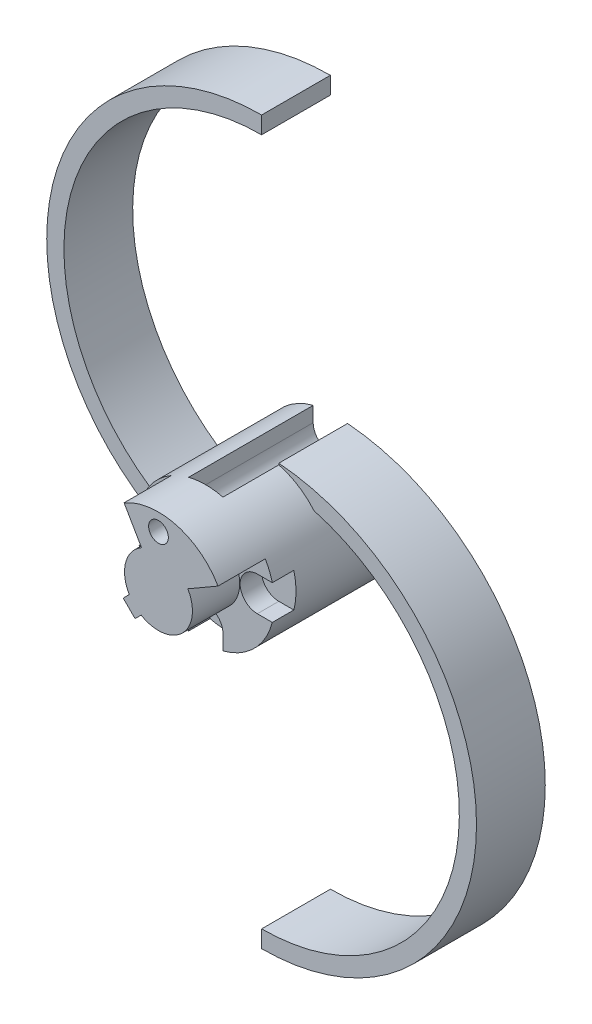
SolidWorks part; units mm, degrees
ref_plane "Front Plane" through (0, 0, 0) normal (0, 0, 1) x (1, 0, 0)
ref_plane "Top Plane" through (0, 0, 0) normal (0, 1, 0) x (1, 0, 0)
ref_plane "Right Plane" through (0, 0, 0) normal (1, 0, 0) x (0, 0, -1)
sketch "Leg-Sketch" plane through (0, 0, 0) normal (0, 0, 1) x (1, 0, 0)
  line L0 (0, 0) -> (0, -42) construction
  line L1 (0, -42) -> (0, -40)
  line L2 (0, 42) -> (0, 40)
  circle A0 centre (0, 0) radius 8 construction
  circle A1 centre (0, 0) radius 6 construction
  circle A2 centre (0, 6) radius 1.15
  circle A3 centre (-6, 0) radius 1.15
  circle A4 centre (0, -6) radius 1.15
  circle A5 centre (6, 0) radius 1.15
  arc A7 (0, 8) -> (0, -42) centre (0, -17) cw
  arc A8 (6.0995, 5.1765) -> (0, -40) centre (0, -17) cw
  arc A9 (0, -8) -> (6.0995, 5.1765) centre (0, 0) ccw
  arc A10 (0, -8) -> (0, 42) centre (0, 17) cw
  arc A11 (0, 40) -> (-6.0995, -5.1765) centre (0, 17) ccw
  arc A12 (0, 8) -> (-6.0995, -5.1765) centre (0, 0) ccw
  point P12 (0, 8)
  dimension "D1" = 16
  dimension "D2" = 12
  dimension "D3" = 2.3
  dimension "D4" = 2
  dimension "D5" = 50
extrude "Leg" add sketch "Leg-Sketch" along normal blind 8
sketch "Hub-Sketch" plane through (0, 0, 0) normal (0, 0, -1) x (-1, 0, 0)
  circle A0 centre (0, 0) radius 8
  circle A1 centre (0, 6) radius 1.15 construction
  circle A2 centre (-6, 0) radius 1.15 construction
  circle A3 centre (0, -6) radius 1.15 construction
  circle A4 centre (6, 0) radius 1.15 construction
  circle A5 centre (0, 6) radius 1.15
  circle A6 centre (-6, 0) radius 1.15
  circle A7 centre (0, -6) radius 1.15
  circle A8 centre (6, 0) radius 1.15
  arc A9 (6.0995, -5.1765) -> (0, 8) centre (0, 0) ccw construction
extrude "Hub" add sketch "Hub-Sketch" along normal blind 12
sketch "Clearance-Sketch" plane through (0, 0, 8) normal (0, 0, 1) x (1, 0, 0)
  line L0 (6, 2) -> (8, 2)
  line L1 (8, 2) -> (8, -2)
  line L2 (8, -2) -> (6, -2)
  line L3 (2, -6) -> (2, -8)
  line L4 (2, -8) -> (-2, -8)
  line L5 (-2, -8) -> (-2, -6)
  line L6 (-6, -2) -> (-8, -2)
  line L7 (-8, -2) -> (-8, 2)
  line L8 (-8, 2) -> (-6, 2)
  line L9 (-2, 6) -> (-2, 8)
  line L10 (-2, 8) -> (2, 8)
  line L11 (2, 8) -> (2, 6)
  circle A0 centre (6, 0) radius 2 construction
  circle A1 centre (0, 6) radius 2 construction
  circle A2 centre (-6, 0) radius 2 construction
  circle A3 centre (0, -6) radius 2 construction
  arc A4 (2, 6) -> (-2, 6) centre (0, 6) cw
  arc A5 (-6, 2) -> (-6, -2) centre (-6, 0) cw
  arc A6 (-2, -6) -> (2, -6) centre (0, -6) cw
  arc A7 (6, -2) -> (6, 2) centre (6, 0) cw
  circle A8 centre (0, 0) radius 8 construction
  dimension "D1" = 4
extrude "Clearance" cut sketch "Clearance-Sketch" against normal offset from surface (14.5 mm away) 5.5 up to face at (-1.15, -6, -12)
sketch "Hub-Cutout-Sketch" plane through (0, 0, -12) normal (0, 0, -1) x (-1, 0, 0)
  line L0 (-3.4208, 1.975) -> (-6.9282, 4)
  line L1 (4, 6.9282) -> (1.975, 3.4208)
  line L7 (2.0172, -3.3961) -> (2.7243, -4.1032)
  line L8 (2.7243, -4.1032) -> (4.1032, -2.7243)
  line L9 (4.1032, -2.7243) -> (3.3961, -2.0172)
  line L10 (0, 0) -> (2.3478, 0) construction
  circle A1 centre (0, 0) radius 8 construction
  arc A2 (-6.9282, 4) -> (4, 6.9282) centre (0, 0) ccw
  arc A3 (-3.4208, 1.975) -> (2.0172, -3.3961) centre (0, 0) ccw
  arc A4 (3.3961, -2.0172) -> (1.975, 3.4208) centre (0, 0) ccw
  dimension "D2" = 3.95
  dimension "D1" = 90
  dimension "D3" = 45
  dimension "D4" = 1
  dimension "D5" = 1.95
  dimension "D6" = 30
extrude "Hub-Cutout" cut sketch "Hub-Cutout-Sketch" against normal up to surface (5.5 mm away) up to face at (4.85, 0, -6.5)
sketch "Cover-Bolts-Sketch" plane through (0, 0, 8) normal (0, 0, 1) x (1, 0, 0)
  line L0 (5.6569, 5.6569) -> (0, 0)
  line L1 (0, 0) -> (-5.6569, 5.6569)
  arc A0 (-5.6569, 5.6569) -> (5.6569, 5.6569) centre (0, 0) ccw
  arc A2 (-2, 7.746) -> (-7.746, 2) centre (0, 0) ccw construction
extrude "Cover-Bolts" add sketch "Cover-Bolts-Sketch" against normal offset from surface (12 mm away) 2.5 up to face at (-0.3679, -1.2187, -6.5)
mirror "Mirror" about plane through (0, 0, 0) normal (0, 0, 1) of bodies 106
delete or keep bodies "KeepMirrorBody" type keep bodies bodies 108
equation "\"D1@Hub\" = \"HUB_WIDTH\""
equation "\"LEG_CLEARANCE\"= 3mm"
equation "\"LEG_WIDTH\"= 8mm"
equation "\"LEG_THICKNESS\"= 2mm"
equation "\"LEG_DIAMETER\"= 50mm"
equation "\"HUB_WIDTH\" = \"LEG_CLEARANCE\" + \"LEG_WIDTH\" + 1mm"
equation "\"D5@Leg-Sketch\" = \"LEG_DIAMETER\""
equation "\"D4@Leg-Sketch\" = \"LEG_THICKNESS\""
equation "\"D1@Leg\"=\"LEG_WIDTH\""
